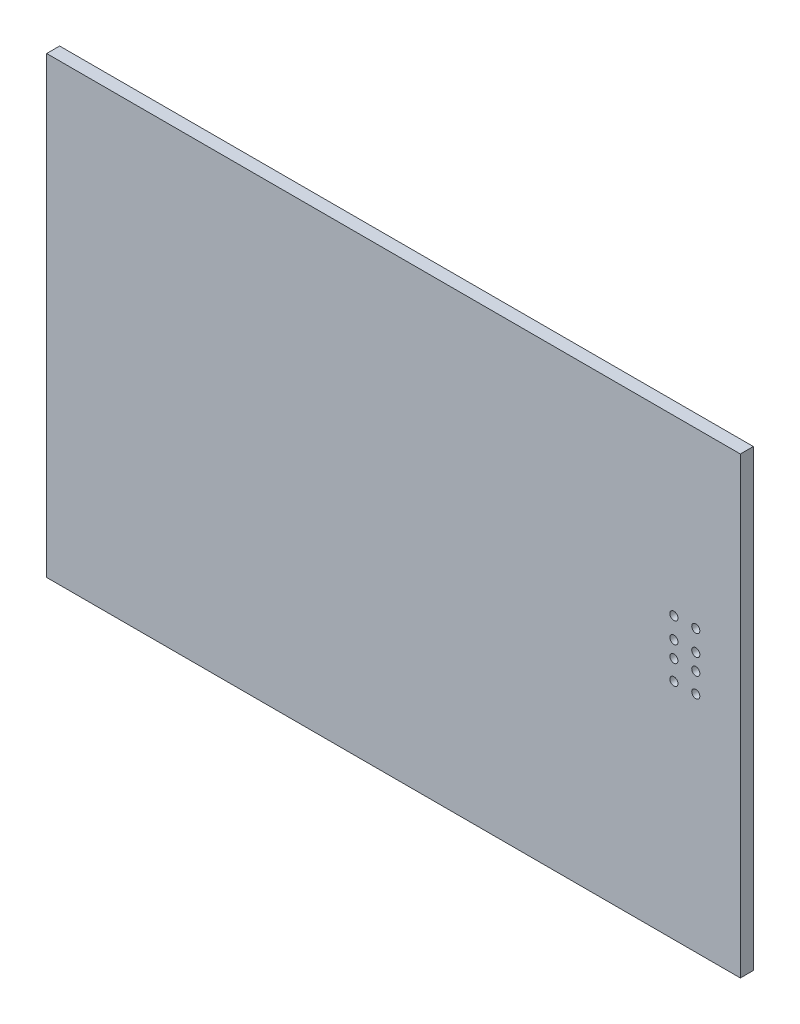
SolidWorks part; units mm, degrees
ref_plane "Plano frontal" through (0, 0, 0) normal (0, 0, 1) x (1, 0, 0)
ref_plane "Plano superior" through (0, 0, 0) normal (0, 1, 0) x (1, 0, 0)
ref_plane "Plano direito" through (0, 0, 0) normal (1, 0, 0) x (0, 0, -1)
ref_plane "Plano1" through (0, 0, 0) normal (0, 0, -1) x (-1, 0, 0)
sketch "Esboço1" plane through (0, 0, 0) normal (0, 0, -1) x (-1, 0, 0)
  line L0 (-42.5, 28) -> (-42.5, -28)
  line L1 (-42.5, -28) -> (43.1, -28)
  line L2 (43.1, -28) -> (43.1, 28)
  line L3 (43.1, 28) -> (-42.5, 28)
  dimension "D1" = 85.6
  dimension "D2" = 56
extrude "Ressalto-extrusão1" add sketch "Esboço1" against normal blind 1.6
sketch "Esboço2" plane through (0, 0, 1.6) normal (0, 0, 1) x (1, 0, 0)
  line L0 (42.5, 28) -> (42.5, -28) construction
  circle A4 centre (37, 6.6) radius 0.5
  circle A5 centre (34.3, 6.6) radius 0.5
  circle A6 centre (34.3, 4.05) radius 0.5
  circle A7 centre (34.3, 2.04) radius 0.5
  circle A8 centre (34.3, -0.4) radius 0.5
  circle A9 centre (37, 4.05) radius 0.5
  circle A10 centre (37, 2.04) radius 0.5
  circle A11 centre (37, -0.4) radius 0.5
  point P18 (42.5, 0)
  dimension "D10" = 5.5
  dimension "D12" = 2.7
  dimension "D14" = 2.55
  dimension "D15" = 2.44
  dimension "D16" = 1
  dimension "D11" = 6.6
extrude "Corte-extrusão1" cut sketch "Esboço2" against normal blind 2
